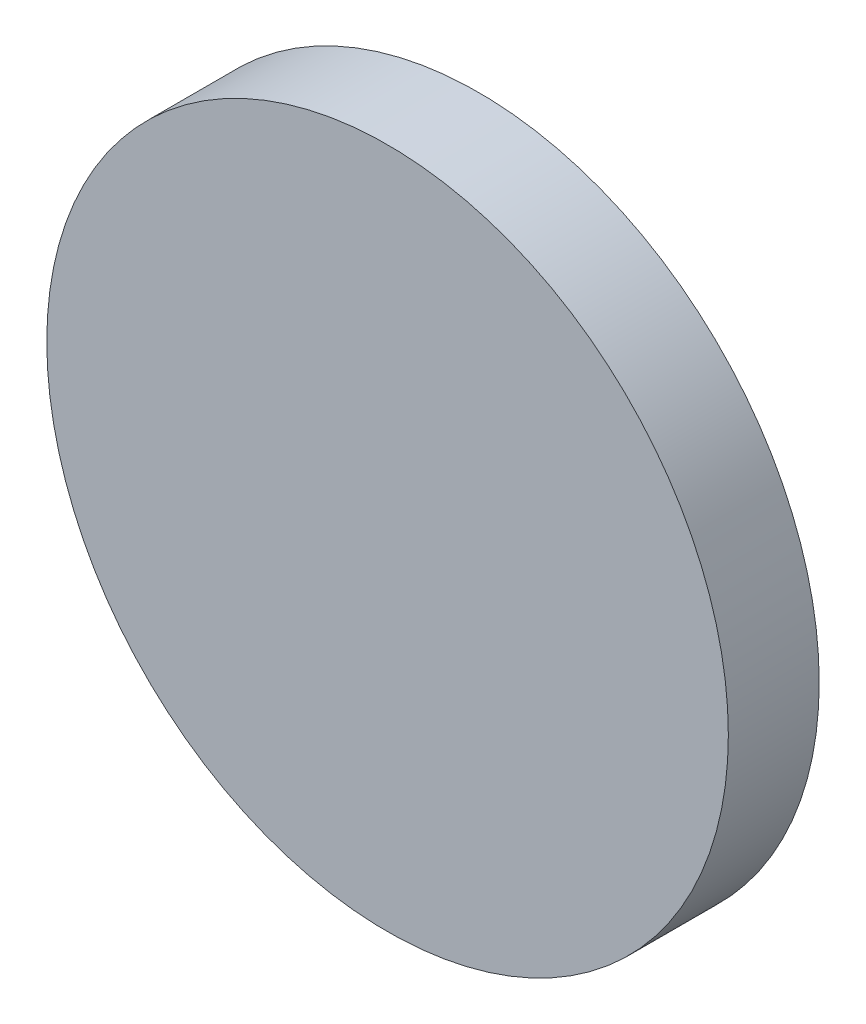
SolidWorks part; units mm, degrees
ref_plane "Front Plane" through (0, 0, 0) normal (0, 0, 1) x (1, 0, 0)
ref_plane "Top Plane" through (0, 0, 0) normal (0, 1, 0) x (1, 0, 0)
ref_plane "Right Plane" through (0, 0, 0) normal (1, 0, 0) x (0, 0, -1)
sketch "Sketch1" plane through (0, 0, 0) normal (0, 0, 1) x (1, 0, 0)
  circle A0 centre (0, 0) radius 75
  dimension "D1" = 150
extrude "Boss-Extrude1" add sketch "Sketch1" along normal blind 20
